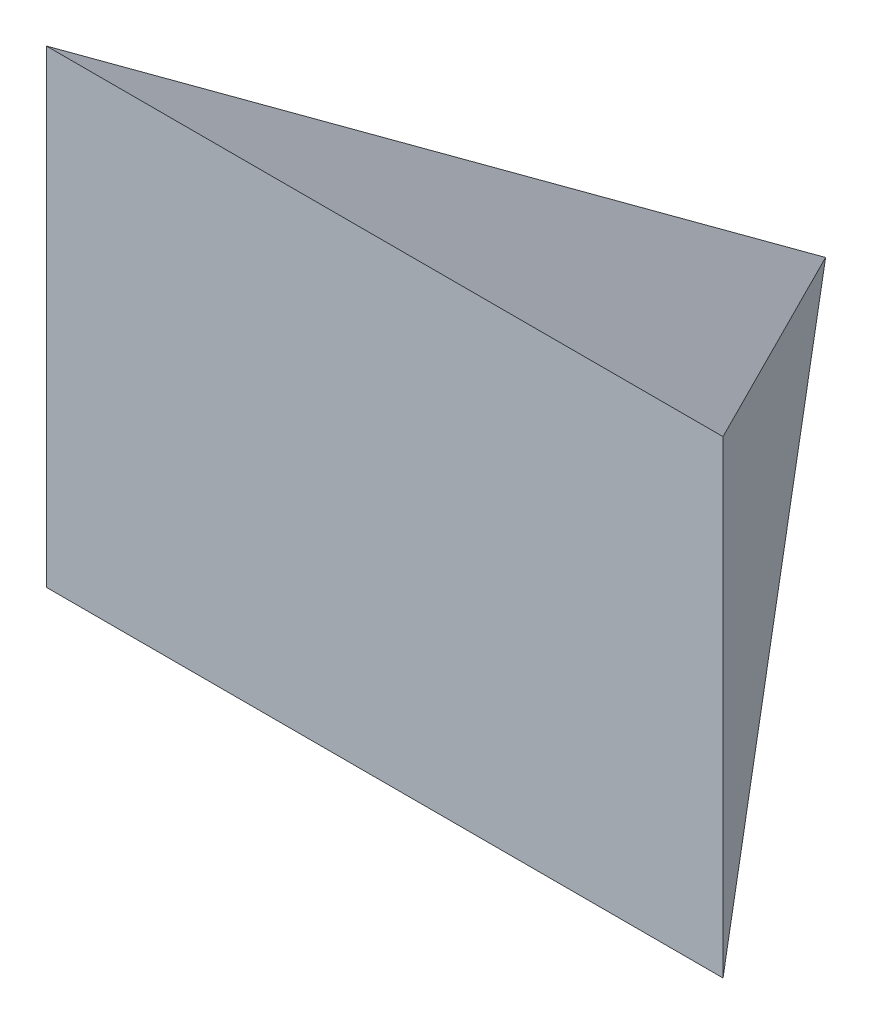
SolidWorks part; units mm, degrees
ref_plane "Front Plane" through (0, 0, 0) normal (0, 0, 1) x (1, 0, 0)
ref_plane "Top Plane" through (0, 0, 0) normal (0, 1, 0) x (1, 0, 0)
ref_plane "Right Plane" through (0, 0, 0) normal (1, 0, 0) x (0, 0, -1)
sketch "Sketch1" plane through (0, 0, 0) normal (0, 1, 0) x (1, 0, 0)
  line L0 (0, 0) -> (-153.4654, -200)
  line L1 (-153.4654, -200) -> (153.4654, -200)
  line L2 (153.4654, -200) -> (0, 0)
  dimension "D1" = 200
  dimension "D2" = 75
extrude "Boss-Extrude1" add sketch "Sketch1" along normal blind 250
sketch "Sketch2" plane through (0, 0, 0) normal (1, 0, 0) x (0, 0, -1)
  line L0 (0, 125) -> (-200, 231.3419)
  line L1 (0, 250) -> (0, 0) construction
  line L2 (-200, 250) -> (-200, 0) construction
  line L3 (-200, 231.3419) -> (-200, 18.6581)
  line L4 (-200, 18.6581) -> (0, 125)
  dimension "D1" = 56
extrude "Cut-Extrude1" cut sketch "Sketch2" against normal through all and the other way through all flip side to cut
